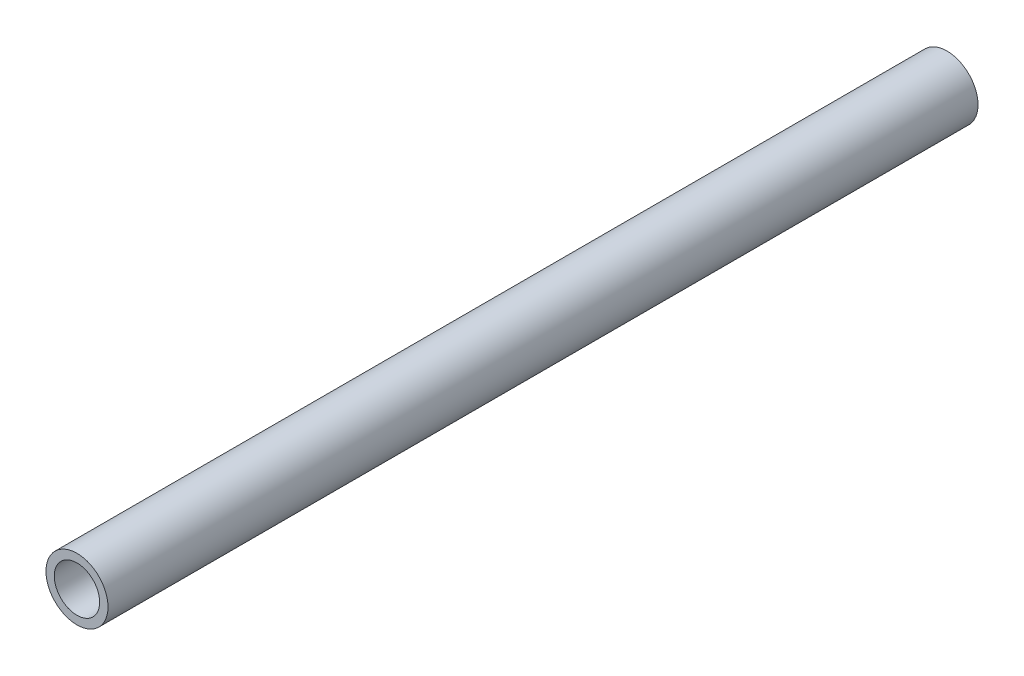
SolidWorks part; units mm, degrees
material "PVC Rígido"
ref_plane "Alzado" through (0, 0, 0) normal (0, 0, 1) x (1, 0, 0)
ref_plane "Planta" through (0, 0, 0) normal (0, 1, 0) x (1, 0, 0)
ref_plane "Vista lateral" through (0, 0, 0) normal (1, 0, 0) x (0, 0, -1)
sketch "Croquis1" plane through (0, 0, 0) normal (0, 0, 1) x (1, 0, 0)
  circle A0 centre (0, 0) radius 10.7
  circle A1 centre (0, 0) radius 7.825
  dimension "D1" = 21.4
  dimension "D2" = 15.65
extrude "Saliente-Extruir1" add sketch "Croquis1" along normal mid plane 300
